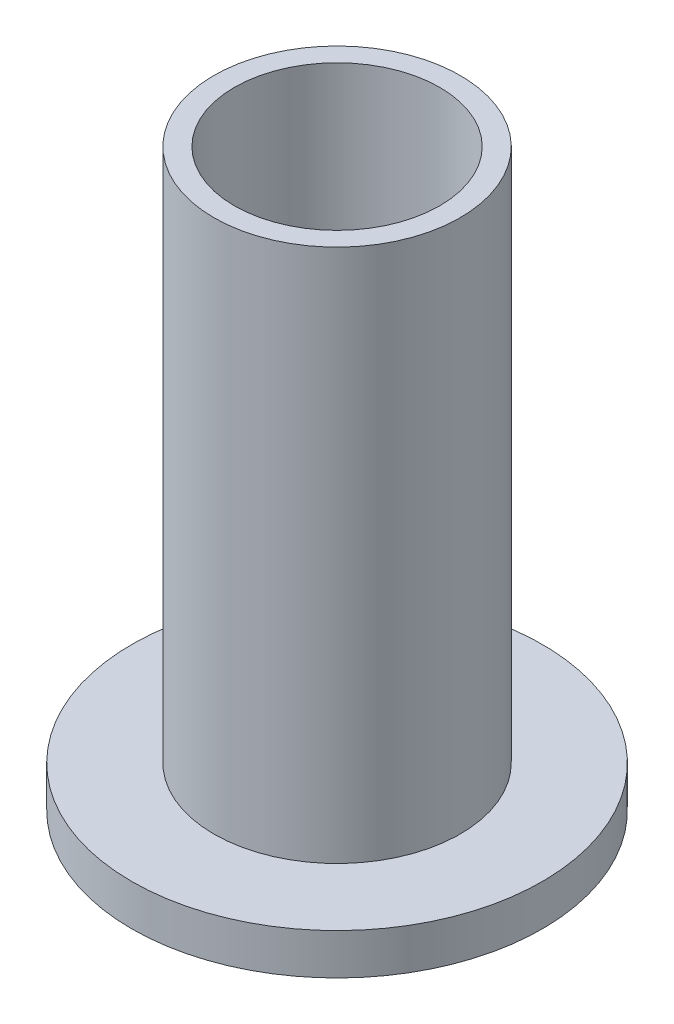
SolidWorks part; units mm, degrees
ref_plane "Front Plane" through (0, 0, 0) normal (0, 0, 1) x (1, 0, 0)
ref_plane "Top Plane" through (0, 0, 0) normal (0, 1, 0) x (1, 0, 0)
ref_plane "Right Plane" through (0, 0, 0) normal (1, 0, 0) x (0, 0, -1)
sketch "Sketch1" plane through (0, 0, 0) normal (0, 0, 1) x (1, 0, 0)
  line L0 (0, 15.2848) -> (0, -14.5886) construction
  line L1 (-5, 17.1456) -> (-5, -10.8544)
  line L2 (-5, -10.8544) -> (-10, -10.8544)
  line L3 (-10, -10.8544) -> (-10, -8.8544)
  line L4 (-10, -8.8544) -> (-6, -8.8544)
  line L5 (-6, -8.8544) -> (-6, 17.1456)
  line L6 (-6, 17.1456) -> (-5, 17.1456)
  dimension "D1" = 5
  dimension "D2" = 6
  dimension "D3" = 10
  dimension "D4" = 2
  dimension "D5" = 26
revolve "Revolve1" add sketch "Sketch1" angle 360 about L0
